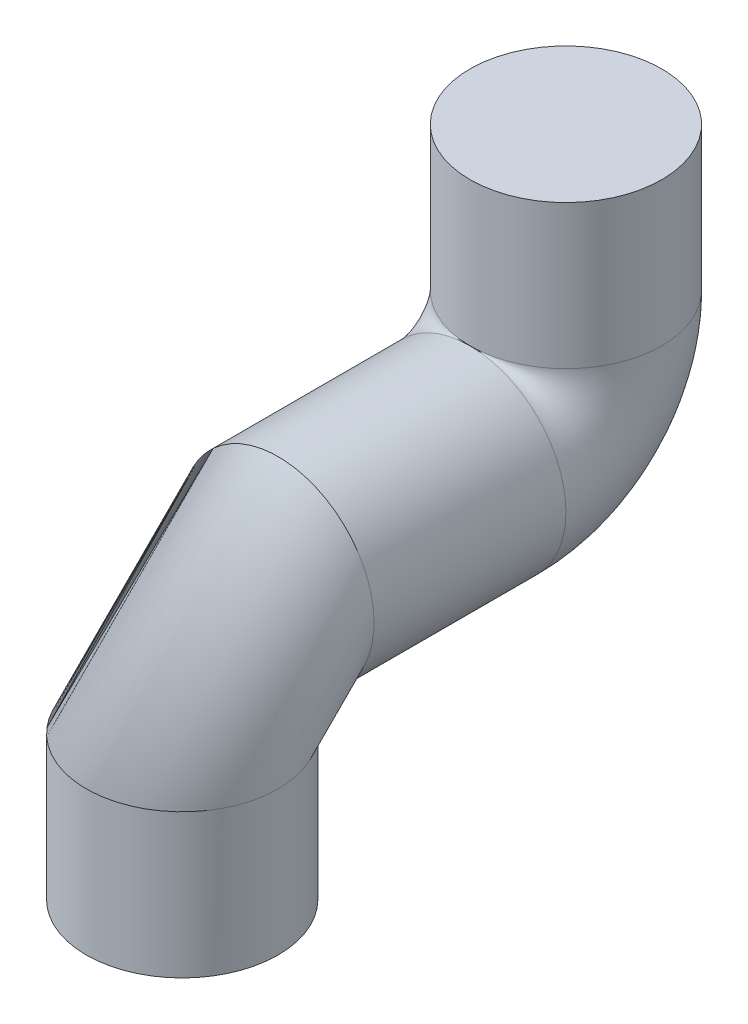
SolidWorks part; units mm, degrees
ref_plane "Front Plane" through (0, 0, 0) normal (0, 0, 1) x (1, 0, 0)
ref_plane "Top Plane" through (0, 0, 0) normal (0, 1, 0) x (1, 0, 0)
ref_plane "Right Plane" through (0, 0, 0) normal (1, 0, 0) x (0, 0, -1)
sketch "Sketch1" plane through (0, 0, 0) normal (1, 0, 0) x (0, 0, -1)
  line L0 (-30, 0) -> (30, 0)
  line L1 (60, 30) -> (60, 75)
  line L2 (-60, -30) -> (-60, -75)
  arc A0 (-30, 0) -> (-60, -30) centre (-30, -30) ccw
  arc A1 (30, 0) -> (60, 30) centre (30, 30) ccw
  point P4 (0, 0)
  point P8 (-60, 0)
  point P11 (60, 0)
  dimension "D4" = 30
  dimension "D1" = 120
  dimension "D2" = 75
  dimension "D3" = 75
ref_plane "Plane1" through (0, 75, 0) normal (0, 1, 0) x (1, 0, 0)
sketch "Sketch3" plane through (0, 75, 0) normal (0, 1, 0) x (1, 0, 0)
  line L0 (0, 0) -> (0, 60) construction
  circle A0 centre (0, 60) radius 30
  dimension "D1" = 60
sweep "Sweep4" add profiles "Sketch3" path "Sketch1"
sketch "Sketch4" plane through (0, -75, 0) normal (0, -1, 0) x (1, 0, 0)
  circle A0 centre (0, 60) radius 20
  dimension "D1" = 40
extrude "Cut-Extrude1" cut sketch "Sketch4" against normal blind 10
